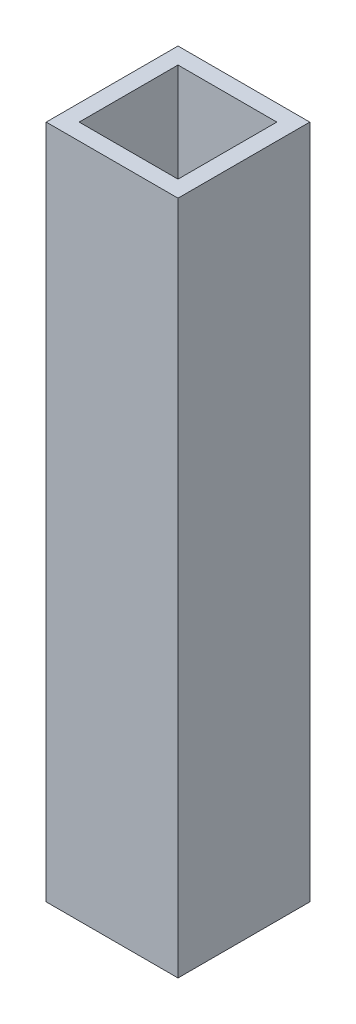
SolidWorks part; units mm, degrees
ref_plane "Front Plane" through (0, 0, 0) normal (0, 0, 1) x (1, 0, 0)
ref_plane "Top Plane" through (0, 0, 0) normal (0, 1, 0) x (1, 0, 0)
ref_plane "Right Plane" through (0, 0, 0) normal (1, 0, 0) x (0, 0, -1)
sketch "Sketch3" plane through (0, 0, 0) normal (0, 1, 0) x (1, 0, 0)
  line L0 (-20, 20) -> (20, 20)
  line L1 (-15, 15) -> (15, 15)
  line L2 (-15, 15) -> (-15, -15)
  line L3 (-15, -15) -> (15, -15)
  line L4 (15, 15) -> (15, -15)
  line L5 (-15, 15) -> (15, -15) construction
  line L6 (-15, -15) -> (15, 15) construction
  line L7 (20, 20) -> (20, -20)
  line L8 (-20, -20) -> (20, -20)
  line L9 (-20, 20) -> (-20, -20)
  point P0 (0, 0)
  dimension "D1" = 30
  dimension "D2" = 30
  dimension "D3" = 5
extrude "Boss-Extrude1" add sketch "Sketch3" along normal blind 205
